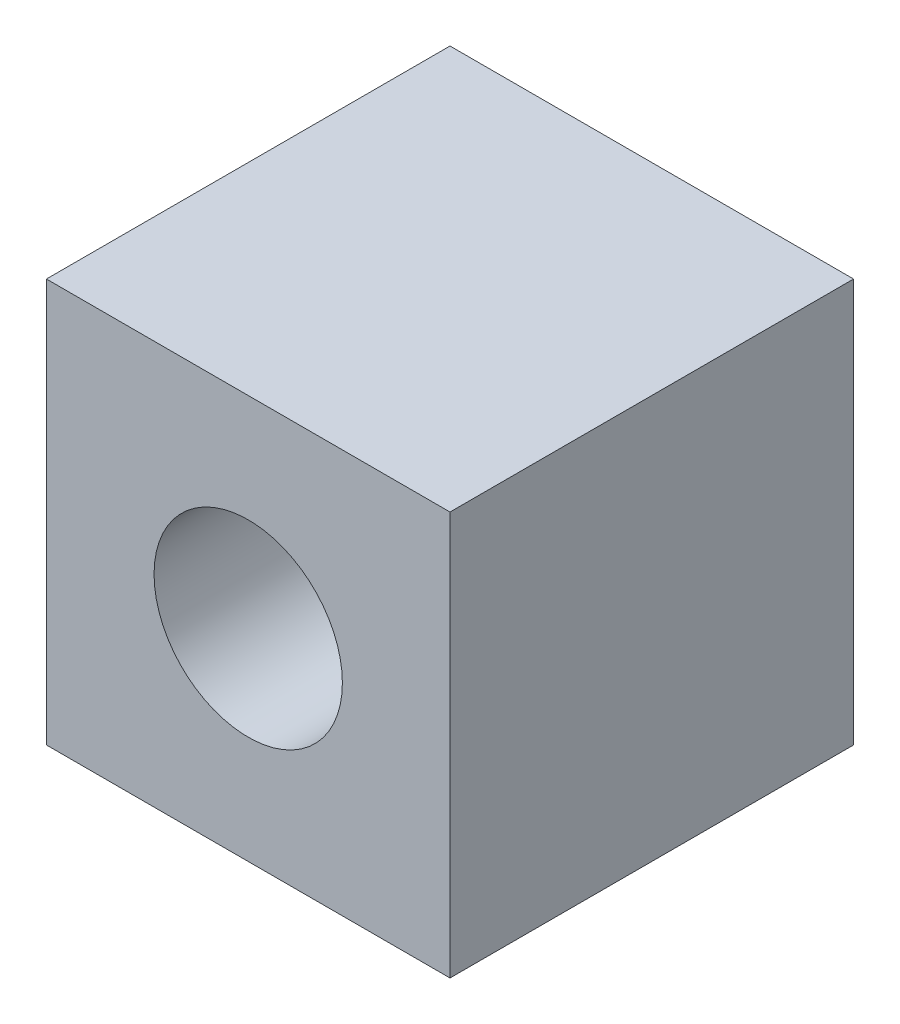
SolidWorks part; units mm, degrees
ref_plane "正面" through (0, 0, 0) normal (0, 0, 1) x (1, 0, 0)
ref_plane "平面" through (0, 0, 0) normal (0, 1, 0) x (1, 0, 0)
ref_plane "右側面" through (0, 0, 0) normal (1, 0, 0) x (0, 0, -1)
sketch "ｽｹｯﾁ1" plane through (0, 0, 0) normal (0, 0, 1) x (1, 0, 0)
  line L1 (-2.7788, 2.893) -> (3.2212, 2.893)
  line L2 (-2.7788, 2.893) -> (-2.7788, -3.107)
  line L3 (-2.7788, -3.107) -> (3.2212, -3.107)
  line L4 (3.2212, 2.893) -> (3.2212, -3.107)
  dimension "D1" = 6
  dimension "D2" = 6
extrude "ﾎﾞｽ - 押し出し1" add sketch "ｽｹｯﾁ1" along normal blind 6
sketch "ｽｹｯﾁ2" plane through (0, 0, 6) normal (0, 0, 1) x (1, 0, 0)
  line L0 (3.2212, 2.893) -> (-2.7788, 2.893) construction
  line L1 (-2.7788, 2.893) -> (-2.7788, -3.107) construction
  circle A0 centre (0.2212, -0.107) radius 1.4
  dimension "D1" = 2.8
  dimension "D2" = 3
  dimension "D3" = 3
extrude "ｶｯﾄ - 押し出し1" cut sketch "ｽｹｯﾁ2" against normal through all
